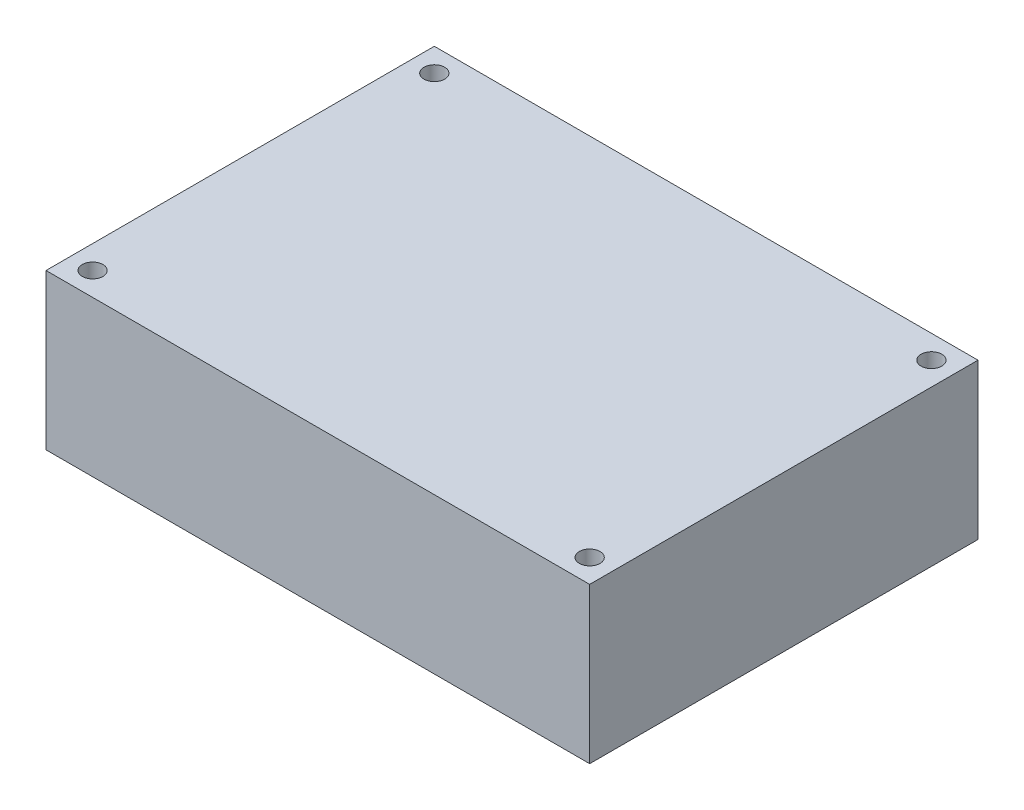
SolidWorks part; units mm, degrees
ref_plane "Front Plane" through (0, 0, 0) normal (0, 0, 1) x (1, 0, 0)
ref_plane "Top Plane" through (0, 0, 0) normal (0, 1, 0) x (1, 0, 0)
ref_plane "Right Plane" through (0, 0, 0) normal (1, 0, 0) x (0, 0, -1)
sketch "Sketch1" plane through (0, 0, 0) normal (0, 1, 0) x (1, 0, 0)
  line L0 (0, 0) -> (0, 119.8276) construction
  line L1 (0, 0) -> (128.4483, 0) construction
  line L3 (-52.5, 37.5) -> (52.5, 37.5)
  line L4 (-52.5, 37.5) -> (-52.5, -37.5)
  line L5 (-52.5, -37.5) -> (52.5, -37.5)
  line L6 (52.5, 37.5) -> (52.5, -37.5)
  point P8 (0, 0)
  point P9 (0, 0)
  dimension "D1" = 75
  dimension "D2" = 105
extrude "Boss-Extrude1" add sketch "Sketch1" along normal mid plane 30
sketch "Sketch2" plane through (0, 15, 0) normal (0, 1, 0) x (1, 0, 0)
  line L0 (0, 0) -> (0, 65.9215) construction
  line L1 (0, 0) -> (63.5244, 0) construction
  point P0 (-48, 33)
  point P1 (-48, -33)
  point P2 (48, 33)
  point P3 (48, -33)
  point P7 (0, 0)
  point P9 (0, 0)
  point P10 (0, 0)
  point P11 (0, 0)
  dimension "D1" = 96
  dimension "D2" = 66
hole_wizard "Ø4.0mm Dowel Hole1" positions "Sketch3" profile "Sketch4" hole size "Ø4.0" standard "ANSI Metric" end condition through all
sketch "Sketch3" plane through (0, 15, 0) normal (0, 1, 0) x (1, 0, 0)
  point P0 (-48, 33)
  point P3 (48, 33)
  point P6 (48, -33)
  point P9 (-48, -33)
sketch "Sketch4" plane through (-48, 15, -33) normal (1, 0, 0) x (0, 0, 1)
  line L0 (0, 0) -> (0, 30)
  line L1 (0, 30) -> (2, 30)
  line L2 (2, 30) -> (2, 0)
  line L5 (2, 0) -> (0, 0)
  line L11 (0, -6.35) -> (0, 107.95) construction
  dimension "Thru Hole Dia." = 4
  dimension "Thru Hole Depth" = 30
